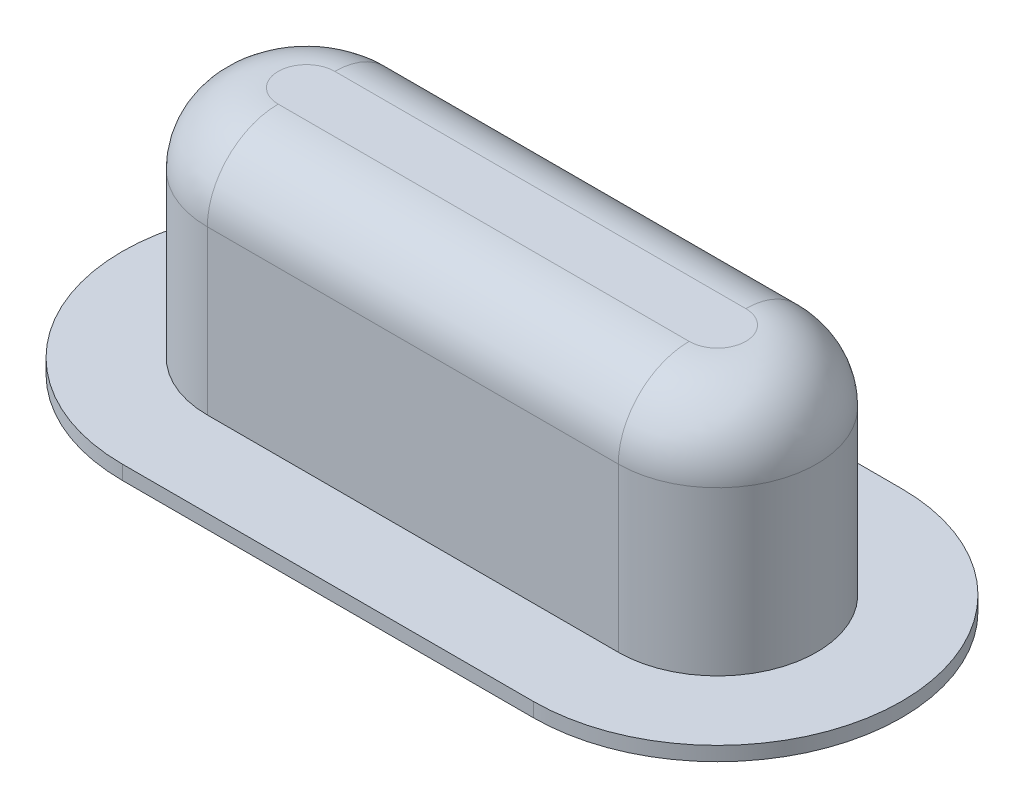
SolidWorks part; units mm, degrees
ref_plane "Front Plane" through (0, 0, 0) normal (0, 0, 1) x (1, 0, 0)
ref_plane "Top Plane" through (0, 0, 0) normal (0, 1, 0) x (1, 0, 0)
ref_plane "Right Plane" through (0, 0, 0) normal (1, 0, 0) x (0, 0, -1)
sketch "Sketch2" plane through (0, 0, 0) normal (0, 1, 0) x (1, 0, 0)
  line L0 (-29, 0) -> (29, 0) construction
  line L1 (-29, 14) -> (29, 14)
  line L2 (-29, -14) -> (29, -14)
  arc A0 (-29, 14) -> (-29, -14) centre (-29, 0) ccw
  arc A1 (29, -14) -> (29, 14) centre (29, 0) ccw
  point P2 (0, 0)
  point P7 (0, 0)
  dimension "D1" = 14
  dimension "D2" = 58
extrude "Boss-Extrude1" add sketch "Sketch2" along normal blind 35
fillet "Fillet1" radius 10 4 edges at (0, 35, -14) (43, 35, 0) (0, 35, 14) (-43, 35, 0)
shell "Shell1" thickness 4
sketch "Sketch3" plane through (0, 0, 0) normal (0, -1, 0) x (1, 0, 0)
  line L2 (-29, -10) -> (29, -10) construction
  line L3 (29, 10) -> (-29, 10) construction
  line L4 (-29, -26) -> (29, -26)
  line L5 (29, 26) -> (-29, 26)
  line L6 (-29, -26) -> (29, -26)
  line L7 (29, 26) -> (-29, 26)
  line L8 (-29, -10) -> (29, -10)
  line L9 (29, 10) -> (-29, 10)
  arc A2 (29, -10) -> (29, 10) centre (29, 0) ccw construction
  arc A3 (-29, 10) -> (-29, -10) centre (-29, 0) ccw construction
  arc A4 (-29, 26) -> (-29, -26) centre (-29, 0) ccw
  arc A5 (29, -26) -> (29, 26) centre (29, 0) ccw
  arc A6 (-29, 26) -> (-29, -26) centre (-29, 0) ccw
  arc A7 (29, -26) -> (29, 26) centre (29, 0) ccw
  arc A8 (29, -10) -> (29, 10) centre (29, 0) ccw
  arc A9 (-29, 10) -> (-29, -10) centre (-29, 0) ccw
  dimension "D1" = 12
extrude "Boss-Extrude2" add sketch "Sketch3" against normal blind 2
sketch "Sketch5" plane through (0, 0, 0) normal (0, -1, 0) x (1, 0, 0)
  line L0 (0, 0) -> (-18.4247, 0) construction
  line L1 (29, -10) -> (-29, -10) construction
  line L5 (0, 0) -> (0, -9.2946) construction
  point P3 (-20, -20)
  point P4 (20, -20)
  point P13 (0, 0)
  point P14 (20, 20)
  point P16 (-20, 20)
  dimension "D1" = 20
  dimension "D2" = 10
hole_wizard "M5 Clearance Hole1" positions "Sketch6" profile "Sketch7" hole size "M5" standard "ANSI Metric"
sketch "Sketch6" plane through (0, 0, 0) normal (0, -1, 0) x (-1, 0, 0)
  point P0 (20, 20)
  point P3 (-20, 20)
  point P6 (-20, -20)
  point P9 (20, -20)
sketch "Sketch7" plane through (-20, 0, -20) normal (1, 0, 0) x (0, 0, -1)
  line L0 (0, 0) -> (0, 2)
  line L1 (0, 2) -> (2.75, 2)
  line L2 (2.75, 2) -> (2.75, 0)
  line L5 (2.75, 0) -> (0, 0)
  line L11 (0, -6.35) -> (0, 107.95) construction
  dimension "Thru Hole Dia." = 5.5
  dimension "Thru Hole Depth" = 2
